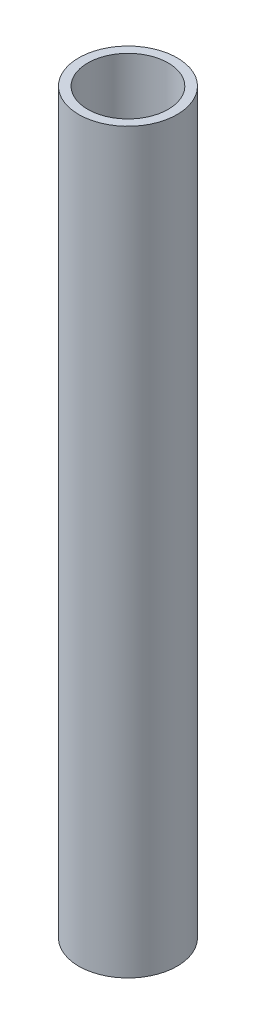
SolidWorks part; units mm, degrees
ref_plane "Plano frontal" through (0, 0, 0) normal (0, 0, 1) x (1, 0, 0)
ref_plane "Plano superior" through (0, 0, 0) normal (0, 1, 0) x (1, 0, 0)
ref_plane "Plano direito" through (0, 0, 0) normal (1, 0, 0) x (0, 0, -1)
sketch "Esboço1" plane through (0, 0, 0) normal (0, 1, 0) x (1, 0, 0)
  circle A0 centre (0, 0) radius 9
  circle A1 centre (0, 0) radius 11
  dimension "D1" = 22
  dimension "D2" = 18
extrude "Ressalto-extrusão1" add sketch "Esboço1" along normal blind 165
